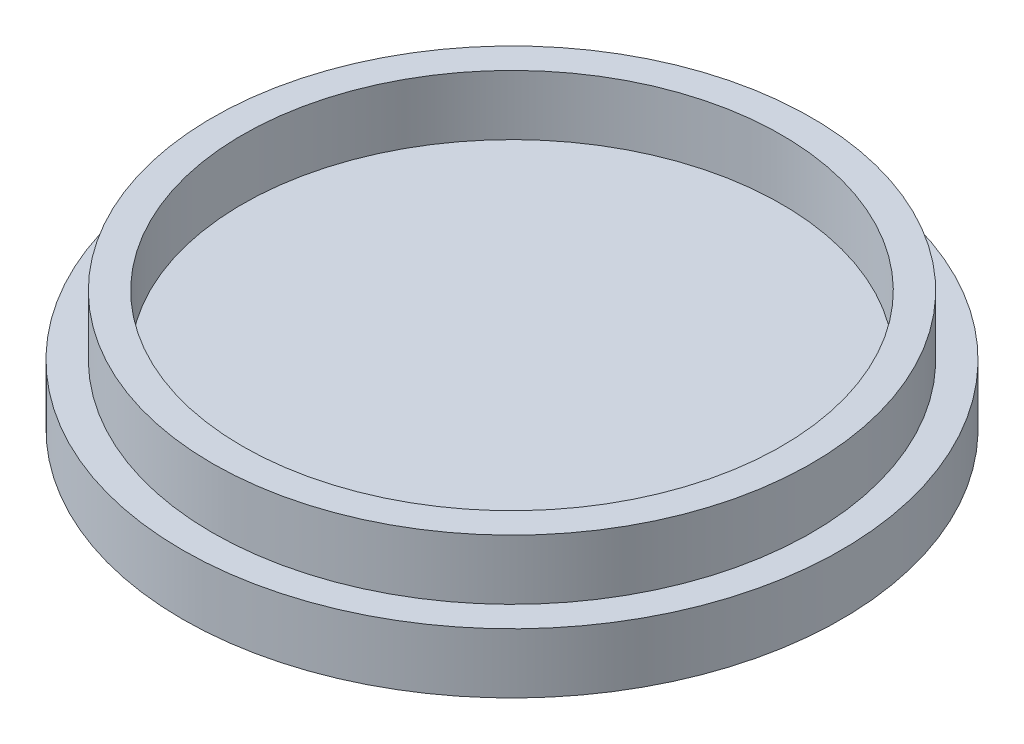
SolidWorks part; units mm, degrees
ref_plane "Front Plane" through (0, 0, 0) normal (0, 0, 1) x (1, 0, 0)
ref_plane "Top Plane" through (0, 0, 0) normal (0, 1, 0) x (1, 0, 0)
ref_plane "Right Plane" through (0, 0, 0) normal (1, 0, 0) x (0, 0, -1)
sketch "Sketch1" plane through (0, 0, 0) normal (0, 1, 0) x (1, 0, 0)
  circle A1 centre (0, 0) radius 27.5
  dimension "D1" = 55
extrude "Boss-Extrude1" add sketch "Sketch1" along normal blind 5 contours A1
sketch "Sketch2" plane through (0, 5, 0) normal (0, 1, 0) x (1, 0, 0)
  circle A0 centre (0, 0) radius 25
  circle A1 centre (0, 0) radius 22.5
  dimension "D1" = 50
  dimension "D2" = 45
extrude "Boss-Extrude2" add sketch "Sketch2" along normal blind 5
